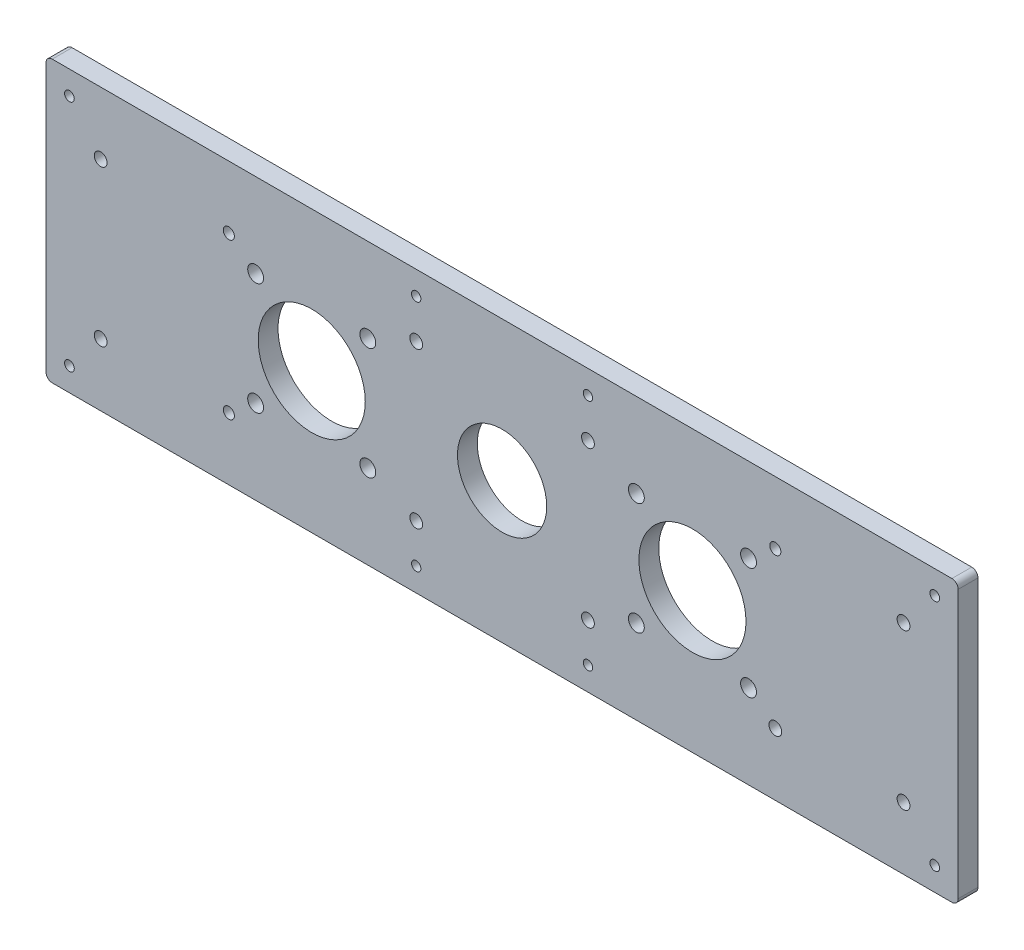
SolidWorks part; units mm, degrees
ref_plane "Front Plane" through (0, 0, 0) normal (0, 0, 1) x (1, 0, 0)
ref_plane "Top Plane" through (0, 0, 0) normal (0, 1, 0) x (1, 0, 0)
ref_plane "Right Plane" through (0, 0, 0) normal (1, 0, 0) x (0, 0, -1)
sketch "Sketch1" plane through (0, 0, 0) normal (0, 0, 1) x (1, 0, 0)
  line L1 (0, 0) -> (292.1, 0)
  line L2 (0, 0) -> (0, 89.8)
  line L3 (0, 89.8) -> (292.1, 89.8)
  line L4 (292.1, 0) -> (292.1, 89.8)
  circle A3 centre (146.05, 44.9) radius 14.2875
  point P7 (146.05, 44.9)
  circle B0 centre (103.0516, 62.8594) radius 2.54
  circle B1 centre (103.0494, 26.9384) radius 2.54
  circle B2 centre (67.1284, 26.9406) radius 2.54
  circle B3 centre (67.1306, 62.8616) radius 2.54
  circle B4 centre (85.09, 44.9) radius 17.145
  circle B5 centre (189.0506, 62.8616) radius 2.54
  circle B6 centre (224.9716, 62.8594) radius 2.54
  circle B7 centre (224.9694, 26.9384) radius 2.54
  circle B8 centre (189.0484, 26.9406) radius 2.54
  circle B9 centre (207.01, 44.9) radius 17.145
  dimension "D3" = 60.96
  dimension "D4" = 60.96
  dimension "D5" = 146.05
  dimension "D6" = 28.575
  dimension "D1" = 89.8
  dimension "D2" = 292.1
sketch_block_instance "Block1-1"
sketch_block "Block1" parameters "D1"=5.08, "D2"=34.29
sketch_block_instance "Block2-1"
sketch_block "Block2" parameters "D1"=5.08, "D2"=34.29
extrude "Boss-Extrude1" add sketch "Sketch1" along normal blind 6.35
sketch "Sketch2" plane through (0, 0, 6.35) normal (0, 0, 1) x (1, 0, 0)
  line L0 (292.1, 89.8) -> (0, 89.8) construction
  line L1 (108.55, 0) -> (183.55, 0)
  line L2 (108.55, 0) -> (108.55, 89.8)
  line L3 (108.55, 89.8) -> (183.55, 89.8)
  line L4 (183.55, 0) -> (183.55, 89.8)
  line L5 (108.55, 0) -> (183.55, 89.8) construction
  line L6 (108.55, 89.8) -> (183.55, 0) construction
  line L7 (108.55, 44.9) -> (146.05, 44.9) construction
  line L8 (108.55, 89.8) -> (-29.3949, 89.8)
  line L9 (108.55, 89.8) -> (108.55, -10.172)
  line L10 (108.55, -10.172) -> (-29.3949, -10.172)
  line L11 (-29.3949, 89.8) -> (-29.3949, -10.172)
  line L12 (183.55, 89.8) -> (343.3103, 89.8)
  line L13 (183.55, 89.8) -> (183.55, -29.3261)
  line L14 (183.55, -29.3261) -> (343.3103, -29.3261)
  line L15 (343.3103, 89.8) -> (343.3103, -29.3261)
  line L16 (146.05, 44.9) -> (146.05, 89.8) construction
  circle A0 centre (118.55, 20) radius 2.05
  circle A1 centre (118.55, 69.8) radius 2.05
  circle A2 centre (173.55, 20) radius 2.05
  circle A3 centre (173.55, 69.8) radius 2.05
  point P0 (146.05, 44.9)
  dimension "D2" = 4.1
  dimension "D3" = 20
  dimension "D1" = 75
  dimension "D4" = 10
extrude "Cut-Extrude1" cut sketch "Sketch2" against normal blind 10 contours A0 | A1 | A3 | A2
sketch "Sketch3" plane through (0, 0, 6.35) normal (0, 0, 1) x (1, 0, 0)
  line L0 (0, 0) -> (292.1, 0) construction
  line L1 (292.1, 0) -> (292.1, 89.8) construction
  line L2 (146.05, 0) -> (146.05, 11.9893) construction
  line L3 (292.1, 44.9) -> (277.1, 44.9) construction
  line L4 (173.55, 20) -> (173.55, 7.5)
  line L5 (173.55, 69.8) -> (173.55, 82.3)
  line L6 (118.55, 20) -> (118.55, 7.5)
  line L7 (118.55, 69.8) -> (118.55, 82.3)
  circle A0 centre (284.6, 7.5) radius 1.55
  circle A1 centre (7.5, 7.5) radius 1.55
  circle A2 centre (7.5, 82.3) radius 1.55
  circle A3 centre (284.6, 82.3) radius 1.55
  circle A4 centre (274.6, 20) radius 2.05
  circle A5 centre (17.5, 20) radius 2.05
  circle A6 centre (17.5, 69.8) radius 2.05
  circle A7 centre (274.6, 69.8) radius 2.05
  circle A8 centre (173.55, 20) radius 2.05 construction
  circle A9 centre (173.55, 7.5) radius 1.5
  circle A10 centre (173.55, 82.3) radius 1.5
  circle A11 centre (118.55, 82.3) radius 1.5
  circle A12 centre (118.55, 7.5) radius 1.5
  dimension "D1" = 3.1
  dimension "D4" = 4.1
  dimension "D7" = 3
  dimension "D8" = 3
  dimension "D9" = 3
  dimension "D10" = 3
  dimension "D2" = 7.5
  dimension "D3" = 7.5
  dimension "D5" = 10
  dimension "D6" = 0
extrude "Cut-Extrude2" cut sketch "Sketch3" against normal blind 10 contours A4 | A0 | A7 | A3 | A6 | A2 | A1 | A5 | A9 | A12 | A10 | A11
fillet "Fillet1" radius 2 4 edges at (0, 0, 3.175) (0, 89.8, 3.175) (292.1, 89.8, 3.175) (292.1, 0, 3.175)
sketch "Sketch4" plane through (0, 0, 6.35) normal (0, 0, 1) x (1, 0, 0)
  line L1 (233.55, 69.8) -> (58.55, 69.8)
  line L2 (233.55, 69.8) -> (233.55, 20)
  line L3 (233.55, 20) -> (58.55, 20)
  line L4 (58.55, 69.8) -> (58.55, 20)
  line L5 (233.55, 69.8) -> (58.55, 20) construction
  line L6 (233.55, 20) -> (58.55, 69.8) construction
  circle A0 centre (233.55, 20) radius 2.05
  circle A1 centre (233.55, 69.8) radius 1.778
  circle A2 centre (58.55, 69.8) radius 1.778
  circle A3 centre (58.55, 20) radius 1.778
  point P0 (146.05, 44.9)
  dimension "D2" = 4.1
  dimension "D3" = 3.556
  dimension "D4" = 3.556
  dimension "D5" = 3.556
  dimension "D1" = 175
extrude "Cut-Extrude4" cut sketch "Sketch4" against normal through all contours A0 | A1 | A2 | A3
scale "Scale1" scale about centroid uniform scaling yes scale factor 0.333333
